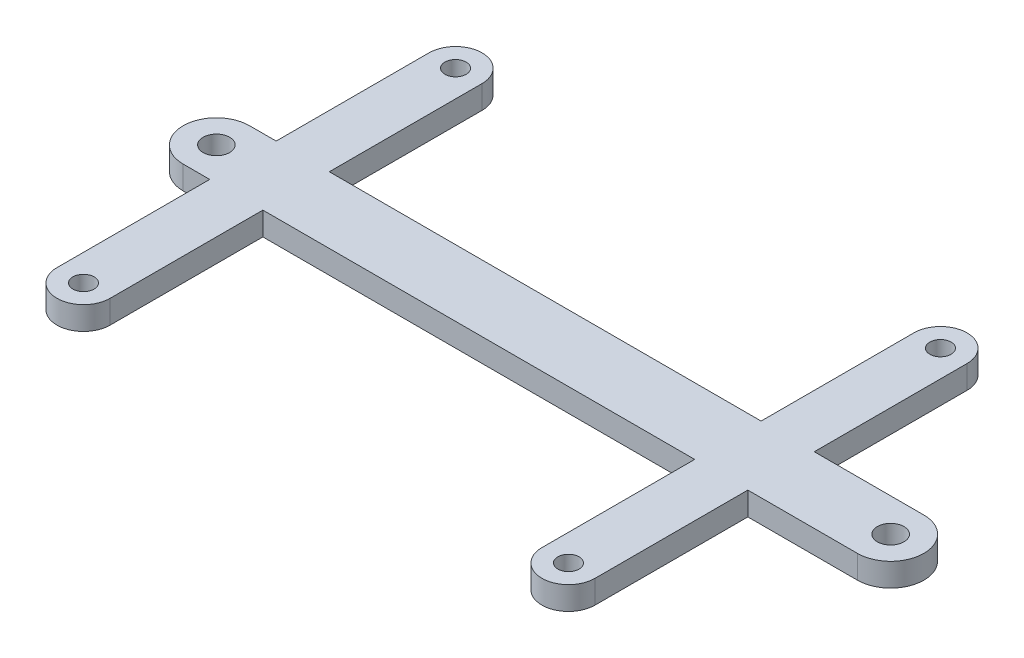
SolidWorks part; units mm, degrees
ref_plane "Front Plane" through (0, 0, 0) normal (0, 0, 1) x (1, 0, 0)
ref_plane "Top Plane" through (0, 0, 0) normal (0, 1, 0) x (1, 0, 0)
ref_plane "Right Plane" through (0, 0, 0) normal (1, 0, 0) x (0, 0, -1)
sketch "Sketch1" plane through (0, 0, 0) normal (0, 1, 0) x (1, 0, 0)
  line L0 (33.5, 28) -> (33.5, 5)
  line L4 (25.5, 28) -> (25.5, 5)
  line L5 (50, 5) -> (33.5, 5)
  line L16 (-51.5, 5) -> (-47.5, 5)
  line L17 (-39.5, 28) -> (-39.5, 5)
  line L18 (-47.5, 28) -> (-47.5, 5)
  line L19 (-39.5, 5) -> (25.5, 5)
  line L20 (0, 0) -> (15.6134, 0)
  line L21 (-39.5, -5) -> (25.5, -5)
  line L22 (-47.5, -28) -> (-47.5, -5)
  line L23 (-39.5, -28) -> (-39.5, -5)
  line L24 (50, -5) -> (33.5, -5)
  line L25 (25.5, -28) -> (25.5, -5)
  line L26 (33.5, -28) -> (33.5, -5)
  line L27 (-47.5, -5) -> (-51.5, -5)
  circle A0 centre (50, 0) radius 2
  arc A1 (50, -5) -> (50, 5) centre (50, 0) ccw
  arc A6 (-51.5, -5) -> (-51.5, 5) centre (-51.5, 0) cw
  circle A7 centre (-51.5, 0) radius 2
  circle A12 centre (29.5, 28) radius 1.6
  arc A13 (33.5, 28) -> (25.5, 28) centre (29.5, 28) ccw
  arc A14 (-39.5, 28) -> (-47.5, 28) centre (-43.5, 28) ccw
  circle A15 centre (-43.5, 28) radius 1.6
  circle A16 centre (-43.5, -28) radius 1.6
  arc A17 (-39.5, -28) -> (-47.5, -28) centre (-43.5, -28) cw
  arc A18 (33.5, -28) -> (25.5, -28) centre (29.5, -28) cw
  circle A19 centre (29.5, -28) radius 1.6
  dimension "D1" = 65
  dimension "D7" = 5
  dimension "D2" = 10
  dimension "D3" = 8
  dimension "D4" = 8
  dimension "D5" = 4
  dimension "D6" = 16.5
extrude "Boss-Extrude1" add sketch "Sketch1" along normal blind 3.5
